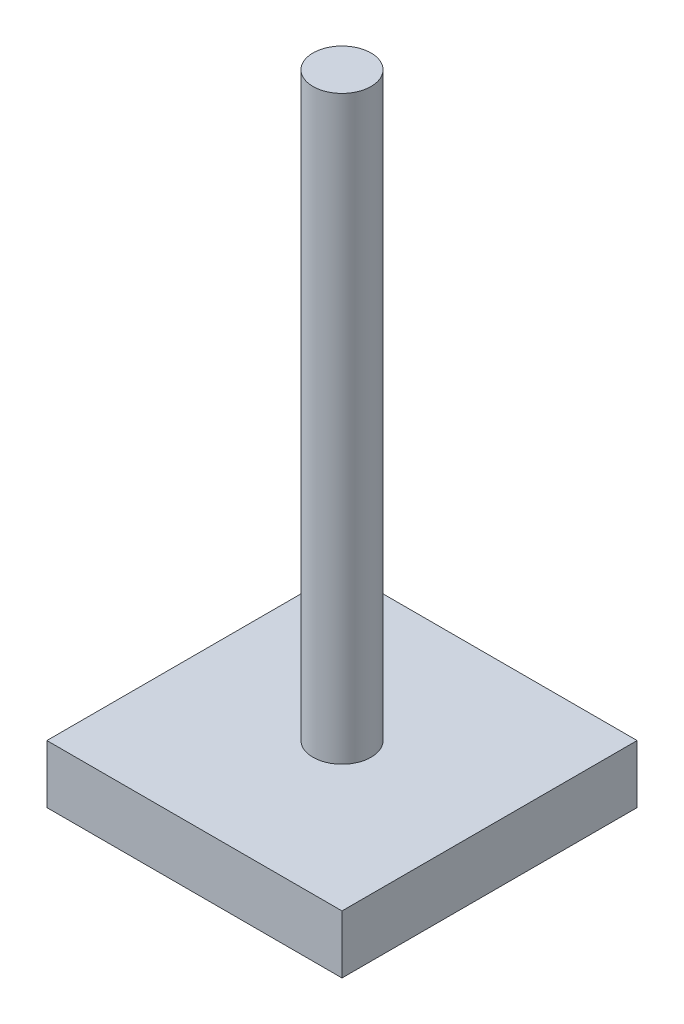
SolidWorks part; units mm, degrees
ref_plane "Front Plane" through (0, 0, 0) normal (0, 0, 1) x (1, 0, 0)
ref_plane "Top Plane" through (0, 0, 0) normal (0, 1, 0) x (1, 0, 0)
ref_plane "Right Plane" through (0, 0, 0) normal (1, 0, 0) x (0, 0, -1)
sketch "Sketch2" plane through (0, 0, 0) normal (0, 1, 0) x (1, 0, 0)
  line L1 (-25.4, -25.4) -> (25.4, -25.4)
  line L2 (-25.4, -25.4) -> (-25.4, 25.4)
  line L3 (-25.4, 25.4) -> (25.4, 25.4)
  line L4 (25.4, -25.4) -> (25.4, 25.4)
  line L5 (-25.4, -25.4) -> (25.4, 25.4) construction
  line L6 (-25.4, 25.4) -> (25.4, -25.4) construction
  point P1 (0, 0)
  dimension "D1" = 50.8
  dimension "D2" = 50.8
extrude "Boss-Extrude1" add sketch "Sketch2" along normal blind 10 contours L2 L3 L4 L1
sketch "Sketch3" plane through (0, 10, 0) normal (0, 1, 0) x (1, 0, 0)
  circle A0 centre (0, 0) radius 5
  dimension "D1" = 10
extrude "Boss-Extrude3" add sketch "Sketch3" along normal blind 100
